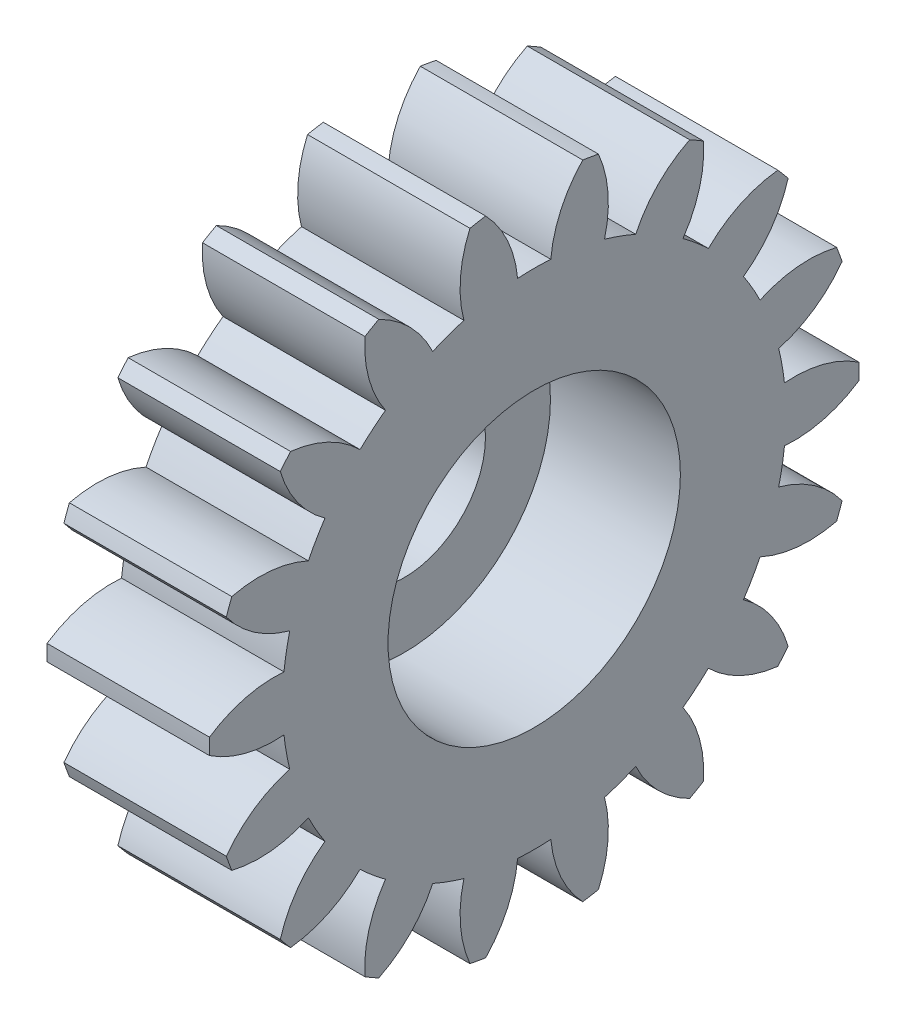
SolidWorks part; units mm, degrees
material "Plain Carbon Steel"
ref_plane "Plane1" through (0, 0, 0) normal (0, 0, 1) x (1, 0, 0)
ref_plane "Plane2" through (0, 0, 0) normal (0, 1, 0) x (1, 0, 0)
ref_plane "Plane3" through (0, 0, 0) normal (1, 0, 0) x (0, 0, -1)
sketch "HoldingSke" plane through (0, 0, 0) normal (0, 1, 0) x (1, 0, 0)
  line L0 (0, 0) -> (0.9511, -0.309)
  line L1 (-15, 0) -> (100, 0) construction
  line L2 (0, 0) -> (-2.1039, 2.3779)
  line L3 (0, 0) -> (-11.863, 4.5341)
  line L4 (0, 0) -> (8.2133, 2.6687)
  line L5 (0, 0) -> (-46.8476, -17.4728)
  line L6 (0, 0) -> (-4.1448, -2.7965)
  line L7 (-2.1039, 2.3779) -> (8.6586, 51.2059)
  line L8 (-76.2, 54.61) -> (-75.3, 54.61)
  line L9 (-71.009, 38.7566) -> (-53.1078, 45.2721)
  line L10 (-76.2, 71.12) -> (104.1128, 71.12)
  line L11 (0, 0) -> (-5, 0)
  line L12 (-76.2, 101.6) -> (-76.162, 101.6)
  line L13 (24.9733, 27.94) -> (52.9518, 28.4284)
  line L14 (24.9733, 27.94) -> (24.9743, 27.94)
  line L15 (24.9733, 27.94) -> (100.4006, 29.5858)
  line L16 (-63.627, -1) -> (-12.827, -1)
  circle A0 centre (0, 0) radius 2.5
  circle A1 centre (0, 0) radius 7.749
  circle A2 centre (0, 0) radius 37.5
  circle A3 centre (0, 0) radius 2.5
  dimension "MHD" = 15.498
  dimension "Hub_dia" = 75
  dimension "Bore" = 5
  dimension "MBD" = 5
  dimension "Num_teeth" = 18
  dimension "Pitch" = 1
  dimension "Overall_len" = 50
  dimension "Show_teeth" = 18
  dimension "Thickness" = 5
  dimension "OAL" = 50.0001
  dimension "T_dim" = 0.9
  dimension "Ap" = 20
  dimension "H" = 19.05
  dimension "Pitch_radius" = 180.3128
  dimension "Width" = 5
  dimension "Backlash" = 0.038
  dimension "Addendum_fac" = 1
  dimension "Dedendum_fac" = 1.25
  dimension "Clearance_fac" = 0.25
  dimension "Dedendum_add" = 0.001
  dimension "Module" = 1
sketch "BasProSke" plane through (0, 0, 0) normal (0, 1, 0) x (1, 0, 0)
  line L0 (-10, 0) -> (60, 0) construction
  line L1 (0, 0) -> (0, 10)
  line L2 (0, 0) -> (5, 0)
  line L3 (5, 0) -> (5, 10)
  line L4 (5, 10) -> (0, 10)
  dimension "Thickness" = 5
  dimension "Diameter" = 20
revolve "Base-Revolve" add sketch "BasProSke" angle 360 about L0
sketch "TooCutSke" plane through (0, 0, 0) normal (1, 0, 0) x (0, 0, -1)
  line L1 (0, 0) -> (0, 107) construction
  line L2 (0, 0) -> (-0.8509, 8.9597) construction
  line L3 (0, 0) -> (-3.1157, 17.6701) construction
  line L4 (-0.8509, 8.9597) -> (-1.5579, 8.835) construction
  arc A0 (0.5106, 7.7322) -> (-0.5106, 7.7322) centre (0, 0) ccw
  arc A1 (1.5152, 9.9102) -> (-1.5152, 9.9102) centre (0, 0) ccw
  circle A2 centre (0, 0) radius 9 construction
  circle A3 centre (0, 0) radius 8.4572 construction
  arc A4 (-0.5106, 7.7322) -> (-1.5152, 9.9102) centre (-4.0952, 7.3996) ccw
  arc A5 (1.5152, 9.9102) -> (0.5106, 7.7322) centre (4.0952, 7.3996) ccw
  dimension "Root_dia" = 15.498
  dimension "Overcut_dia" = 20.0508
  dimension "Pitch_dia" = 18
  dimension "Base_dia" = 16.9145
  dimension "Flank_rad" = 3.6
  dimension "Half_ang" = 10
  dimension "Half_CT" = 0.7179
extrude "ToothCut" cut sketch "TooCutSke" along normal through all
fillet "Breaks" [suppressed] radius 0.02
fillet "RootFillets" [suppressed] radius 0.251
pattern_circular "TeethCuts" count 18 every 20 about axis through (-10, 0, 0) along (1, 0, 0) of "ToothCut", "RootFillets", "Breaks"
sketch "HubNeaOneSke" plane through (0, 0, 0) normal (-1, 0, 0) x (0, 0, 1)
  circle A0 centre (0, 0) radius 7.749
  dimension "Diameter" = 15.498
extrude "HubNearOne" [suppressed] add sketch "HubNeaOneSke" along normal blind 45.0001
sketch "HubNeaBotSke" plane through (0, 0, 0) normal (-1, 0, 0) x (0, 0, 1)
  circle A0 centre (0, 0) radius 7.749
  dimension "Diameter" = 15.498
extrude "HubNearBoth" [suppressed] add sketch "HubNeaBotSke" along normal blind 22.5
ref_plane "FarPln" through (5, 0, 0) normal (1, 0, 0) x (0, 0, -1)
sketch "HubFarSke" plane through (5, 0, 0) normal (1, 0, 0) x (0, 0, -1)
  circle A0 centre (0, 0) radius 7.749
  dimension "Diameter" = 15.498
extrude "HubFar" [suppressed] add sketch "HubFarSke" along normal blind 22.5
sketch "BorSke" plane through (0, 0, 0) normal (1, 0, 0) x (0, 0, -1)
  circle A0 centre (0, 0) radius 2.5
  dimension "Diameter" = 5
extrude "Bore" cut sketch "BorSke" along normal mid plane 100.0001
sketch "KeySke" plane through (0, 0, 0) normal (1, 0, 0) x (0, 0, -1)
  line L0 (-1, 0) -> (-1, 3.4)
  line L1 (-1, 3.4) -> (1, 3.4)
  line L2 (1, 3.4) -> (1, 0)
  line L3 (0, 0) -> (0, 34) construction
  line L4 (-1, 0) -> (1, 0)
  dimension "Offset" = 3.4
  dimension "Width" = 2
extrude "Keyway" [suppressed] cut sketch "KeySke" along normal mid plane 100.0001
pattern_circular "Keyway2" [suppressed] count 2 every 90 about axis through (-10, 0, 0) along (1, 0, 0)
sketch "Sketch1" plane through (5, 0, 0) normal (1, 0, 0) x (0, 0, -1)
  circle A0 centre (0, 0) radius 4.5
  dimension "D1" = 9
extrude "Cut-Extrude1" cut sketch "Sketch1" against normal blind 4
sketch "Sketch2" plane through (0, 0, 0) normal (-1, 0, 0) x (0, 0, 1)
  point P0 (0, 0)
equation "' \"Module@HoldingSke\" = 6.35"
equation "' \"Num_teeth@HoldingSke\" = 12"
equation "' \"Ap@HoldingSke\" =  20"
equation "' \"Ap@HoldingSke\" = 20"
equation "' \"Width@HoldingSke\" = 0.5 * 25.4"
equation "' \"Hub_dia@HoldingSke\"= 1 * 25.4"
equation "' \"Hub_dia@HoldingSke\" = 1 * 25.4"
equation "' \"Overall_len@HoldingSke\" = 1.0 * 25.4"
equation "' \"Bore@HoldingSke\" = 0.75 * 25.4"
equation "' \"T_dim@HoldingSke\" = 0.1 * 25.4"
equation "' \"Width@KeySke\" = 0.25 * 25.4"
equation "' \"Show_teeth@HoldingSke\" = 13"
equation "' \"Backlash@HoldingSke\" = 0.009 * 25.4"
equation "' \"Addendum_fac@HoldingSke\" = 1.0"
equation "' \"Dedendum_fac@HoldingSke\" = 1.25"
equation "' \"Dedendum_add@HoldingSke\" = 0.00005 * 25.4"
equation "' \"Clearance_fac@HoldingSke\" = 0.25"
equation "\"Pitch@HoldingSke\" = 1 / \"Module@HoldingSke\""
equation "\"Overcut_dia@TooCutSke\" = (\"Num_teeth@HoldingSke\" + 2 * \"Addendum_fac@HoldingSke\") / \"Pitch@HoldingSke\" + 0.002 * 25.4"
equation "\"Pitch_dia@TooCutSke\" = \"Num_teeth@HoldingSke\" / \"Pitch@HoldingSke\""
equation "\"Base_dia@TooCutSke\" = \"Num_teeth@HoldingSke\" / \"Pitch@HoldingSke\" * cos((\"Ap@HoldingSke\"  * 3.14159265 / 180))"
equation "\"Root_dia@TooCutSke\" = (\"Num_teeth@HoldingSke\" + 2) / \"Pitch@HoldingSke\" - 2 * (\"Addendum_fac@HoldingSke\" + \"Dedendum_fac@HoldingSke\") / \"Pitch@HoldingSke\" - \"Dedendum_add@HoldingSke\" * 2"
equation "\"Half_ang@TooCutSke\" = 180 / \"Num_teeth@HoldingSke\""
equation "\"Half_CT@TooCutSke\" = \"Num_teeth@HoldingSke\" / \"Pitch@HoldingSke\" * sin((3.14159265 / 2 / \"Num_teeth@HoldingSke\")) / 2 - 7 * \"Backlash@HoldingSke\" / 4"
equation "\"Flank_rad@TooCutSke\" = \"Num_teeth@HoldingSke\" / \"Pitch@HoldingSke\" / 5"
equation "\"Radius@RootFillets\" = \"Clearance_fac@HoldingSke\" / \"Pitch@HoldingSke\" + \"Dedendum_add@HoldingSke\""
equation "\"Break_rad@Breaks\" = 0.02 / \"Pitch@HoldingSke\""
equation "\"Thickness@HoldingSke\" = \"Width@HoldingSke\""
equation "\"OAL@HoldingSke\" = \"Thickness@HoldingSke\""
equation "\"MHD@HoldingSke\" = (\"Num_teeth@HoldingSke\" + 2) / \"Pitch@HoldingSke\" - 2 * (\"Addendum_fac@HoldingSke\" + \"Dedendum_fac@HoldingSke\")  / \"Pitch@HoldingSke\" - \"Dedendum_add@HoldingSke\" * 2"
equation "\"MBD@HoldingSke\" = (\"Num_teeth@HoldingSke\" + 2) / \"Pitch@HoldingSke\" - 2 * (\"Addendum_fac@HoldingSke\" + \"Dedendum_fac@HoldingSke\")  / \"Pitch@HoldingSke\" - \"Dedendum_add@HoldingSke\" * 2 - 0.002 * 25.4"
equation "\"MHD@HoldingSke\" = ((sgn( \"MHD@HoldingSke\" - \"Hub_dia@HoldingSke\" )-1)*( \"MHD@HoldingSke\" - \"Hub_dia@HoldingSke\" ))/-2+ \"Hub_dia@HoldingSke\""
equation "\"MBD@HoldingSke\" = ((sgn( \"MBD@HoldingSke\" - \"Bore@HoldingSke\" )-1)*( \"MBD@HoldingSke\" - \"Bore@HoldingSke\" ))/-2+ \"Bore@HoldingSke\""
equation "\"OAL@HoldingSke\" = ((sgn( \"OAL@HoldingSke\" - \"Overall_len@HoldingSke\" )+1)*( \"OAL@HoldingSke\" - \"Overall_len@HoldingSke\" ))/2 + \"Overall_len@HoldingSke\" + 0.000002 * 25.4"
equation "\"Num_teeth@TeethCuts\" = int( \"Show_teeth@HoldingSke\" ) + 1"
equation "\"Num_teeth@TeethCuts\" = ((sgn( \"Num_teeth@TeethCuts\" - \"Num_teeth@HoldingSke\" )-1)*( \"Num_teeth@TeethCuts\" - \"Num_teeth@HoldingSke\" ))/-2+ \"Num_teeth@HoldingSke\""
equation "\"Num_teeth@TeethCuts\" = ((sgn( \"Num_teeth@TeethCuts\" - 2.0)+1)*( \"Num_teeth@TeethCuts\" - 2.0))/2 +2.0"
equation "\"Angle@TeethCuts\" = 360.0 / \"Num_teeth@HoldingSke\""
equation "\"Diameter@BasProSke\" = (\"Num_teeth@HoldingSke\" + 2 * \"Addendum_fac@HoldingSke\") / \"Pitch@HoldingSke\""
equation "\"Thickness@BasProSke\"  = \"Thickness@HoldingSke\""
equation "' \"Fillet_rad@BasProSke\" =  \"Thickness@HoldingSke\" * 0.05"
equation "' \"Fillet_rad@BasProSke\" = \"Thickness@HoldingSke\" * 0.05"
equation "\"MHD@HoldingSke\" = ((sgn( \"MHD@HoldingSke\" - \"Root_dia@TooCutSke\" )-1)*( \"MHD@HoldingSke\" - \"Root_dia@TooCutSke\" ))/-2+ \"Root_dia@TooCutSke\""
equation "\"Diameter@HubNeaOneSke\" = \"MHD@HoldingSke\""
equation "\"Length@HubNearOne\" = \"OAL@HoldingSke\" - \"Thickness@BasProSke\""
equation "\"Diameter@HubNeaBotSke\" = \"MHD@HoldingSke\""
equation "\"Length@HubNearBoth\" = ( \"OAL@HoldingSke\" - \"Thickness@BasProSke\" ) / 2.0"
equation "\"Thickness@FarPln\" = \"Thickness@BasProSke\""
equation "\"Diameter@HubFarSke\" = \"MHD@HoldingSke\""
equation "\"Length@HubFar\" = ( \"OAL@HoldingSke\" - \"Thickness@BasProSke\" ) / 2.0"
equation "\"Diameter@BorSke\" = \"MBD@HoldingSke\""
equation "\"D1@Bore\" = \"OAL@HoldingSke\" * 2.0"
equation "\"D1@Keyway\" = \"OAL@HoldingSke\" * 2.0"
equation "\"Offset@KeySke\" = \"T_dim@HoldingSke\" + \"MBD@HoldingSke\" / 2.0"
